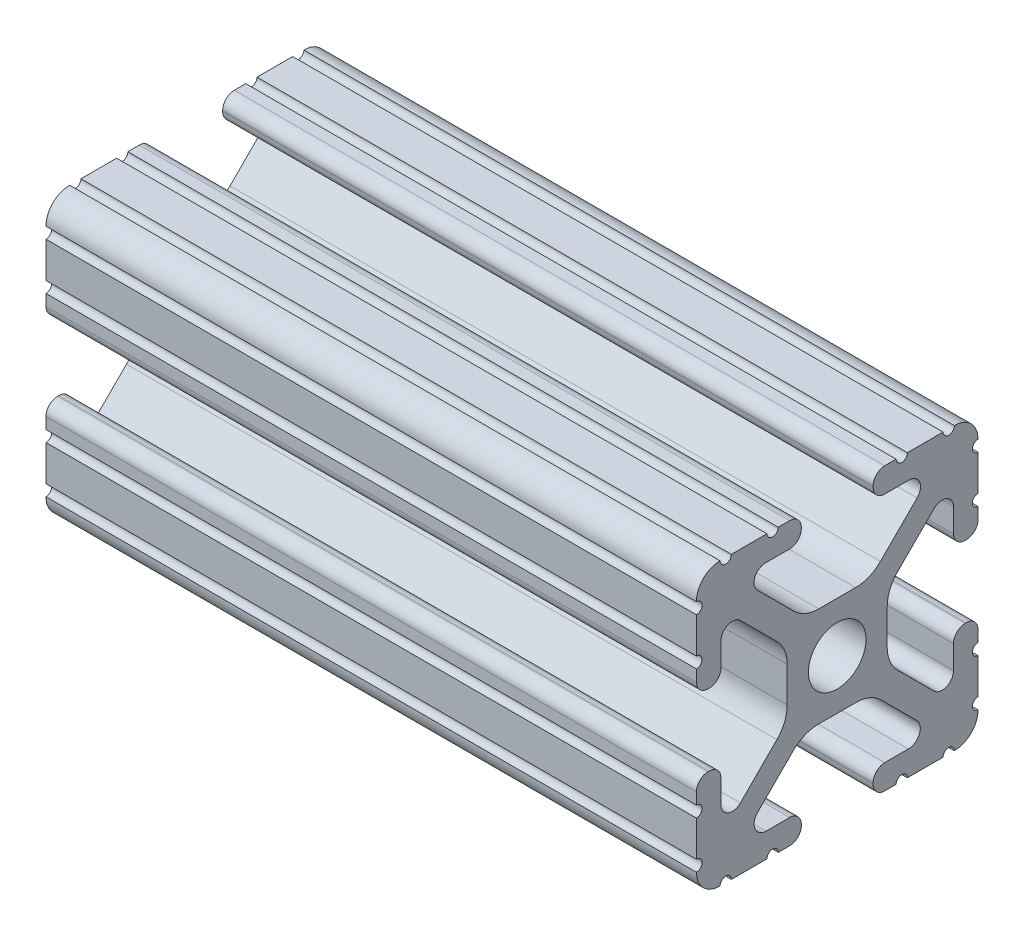
SolidWorks part; units mm, degrees
ref_plane "Front Plane" through (0, 0, 0) normal (0, 0, 1) x (1, 0, 0)
ref_plane "Top Plane" through (0, 0, 0) normal (0, 1, 0) x (1, 0, 0)
ref_plane "Right Plane" through (0, 0, 0) normal (1, 0, 0) x (0, 0, -1)
sketch "Sketch1" plane through (0, 0, 0) normal (0, 1, 0) x (1, 0, 0)
  line L0 (0, 0) -> (-58.674, 0)
  dimension "D1" = 58.674
other "10 1010 PROFILE(1)"
ref_plane "Plane1" through (0, 0, 0) normal (-1, 0, 0) x (0, 0, 1)
sketch "Sketch11" plane through (0, 0, 0) normal (-1, 0, 0) x (0, 0, 1)
  line L1 (12.7, 12.7) -> (-12.7, 12.7) construction
  line L2 (12.7, 12.7) -> (12.7, -12.7) construction
  line L3 (12.7, -12.7) -> (-12.7, -12.7) construction
  line L4 (-12.7, 12.7) -> (-12.7, -12.7) construction
  line L5 (12.7, 12.7) -> (-12.7, -12.7) construction
  line L6 (12.7, -12.7) -> (-12.7, 12.7) construction
  line L88 (-1.7093, -4.4958) -> (1.7093, -4.4958)
  line L89 (3.9523, -5.4237) -> (7.1797, -8.6452)
  line L90 (6.4164, -10.4902) -> (4.2875, -10.4902)
  line L91 (3.2385, -11.5392) -> (3.2385, -11.651)
  line L92 (4.2875, -12.7) -> (5.3171, -12.7)
  line L93 (6.3331, -12.7) -> (9.5504, -12.7)
  line L94 (12.7, -9.5504) -> (12.7, -6.3331)
  line L95 (12.7, -5.3171) -> (12.7, -4.2875)
  line L96 (11.651, -3.2385) -> (11.5392, -3.2385)
  line L97 (10.4902, -4.2875) -> (10.4902, -6.4021)
  line L98 (8.737, -7.1292) -> (5.4405, -3.8388)
  line L99 (4.5085, -1.5917) -> (4.5085, 1.5917)
  line L100 (5.4405, 3.8388) -> (8.737, 7.1292)
  line L101 (10.4902, 6.4021) -> (10.4902, 4.2875)
  line L102 (11.5392, 3.2385) -> (11.651, 3.2385)
  line L103 (12.7, 4.2875) -> (12.7, 5.3171)
  line L104 (12.7, 6.3331) -> (12.7, 9.5504)
  line L105 (9.5504, 12.7) -> (6.3331, 12.7)
  line L106 (5.3171, 12.7) -> (4.2875, 12.7)
  line L107 (3.2384, 11.651) -> (3.2384, 11.5392)
  line L108 (4.2875, 10.4902) -> (6.4768, 10.4902)
  line L109 (7.2072, 8.7245) -> (3.9003, 5.4237)
  line L110 (1.6573, 4.4958) -> (-1.6573, 4.4958)
  line L111 (-3.9003, 5.4237) -> (-7.2072, 8.7245)
  line L112 (-6.4768, 10.4902) -> (-4.2875, 10.4902)
  line L113 (-3.2384, 11.5392) -> (-3.2384, 11.651)
  line L114 (-4.2875, 12.7) -> (-5.3171, 12.7)
  line L115 (-6.3331, 12.7) -> (-9.5504, 12.7)
  line L116 (-12.7, 9.5504) -> (-12.7, 6.3331)
  line L117 (-12.7, 5.3171) -> (-12.7, 4.2875)
  line L118 (-11.651, 3.2385) -> (-11.5392, 3.2385)
  line L119 (-10.4902, 4.2875) -> (-10.4902, 6.4021)
  line L120 (-8.737, 7.1292) -> (-5.4405, 3.8388)
  line L121 (-4.5085, 1.5917) -> (-4.5085, -1.5917)
  line L122 (-5.4405, -3.8388) -> (-8.737, -7.1292)
  line L123 (-10.4902, -6.4021) -> (-10.4902, -4.2875)
  line L124 (-11.5392, -3.2385) -> (-11.651, -3.2385)
  line L125 (-12.7, -4.2875) -> (-12.7, -5.3171)
  line L126 (-12.7, -6.3331) -> (-12.7, -9.5504)
  line L127 (-9.5504, -12.7) -> (-6.3331, -12.7)
  line L128 (-5.3171, -12.7) -> (-4.2875, -12.7)
  line L129 (-3.2385, -11.651) -> (-3.2385, -11.5392)
  line L130 (-4.2875, -10.4902) -> (-6.4164, -10.4902)
  line L131 (-7.1797, -8.6452) -> (-3.9523, -5.4237)
  circle A1 centre (0, 0) radius 2.6035
  arc A104 (-1.7093, -4.4958) -> (-3.9523, -5.4237) centre (-1.7093, -7.6708) ccw
  arc A105 (3.9523, -5.4237) -> (1.7093, -4.4958) centre (1.7093, -7.6708) ccw
  arc A106 (6.4164, -10.4902) -> (7.1797, -8.6452) centre (6.4164, -9.4098) ccw
  arc A107 (4.2875, -10.4902) -> (3.2385, -11.5392) centre (4.2875, -11.5392) ccw
  arc A108 (3.2385, -11.651) -> (4.2875, -12.7) centre (4.2875, -11.651) ccw
  arc A109 (6.3331, -12.7) -> (5.3171, -12.7) centre (5.8251, -12.7) ccw
  arc A110 (10.5664, -12.6998) -> (9.5504, -12.7) centre (10.0584, -12.7) ccw
  arc A111 (10.5664, -12.6998) -> (12.6998, -10.5664) centre (10.5918, -10.5918) ccw
  arc A112 (12.7, -9.5504) -> (12.6998, -10.5664) centre (12.7, -10.0584) ccw
  arc A113 (12.7, -5.3171) -> (12.7, -6.3331) centre (12.7, -5.8251) ccw
  arc A114 (12.7, -4.2875) -> (11.651, -3.2385) centre (11.651, -4.2875) ccw
  arc A115 (11.5392, -3.2385) -> (10.4902, -4.2875) centre (11.5392, -4.2875) ccw
  arc A116 (8.737, -7.1292) -> (10.4902, -6.4021) centre (9.4628, -6.4021) ccw
  arc A117 (4.5085, -1.5917) -> (5.4405, -3.8388) centre (7.6835, -1.5917) ccw
  arc A118 (5.4405, 3.8388) -> (4.5085, 1.5917) centre (7.6835, 1.5917) ccw
  arc A119 (10.4902, 6.4021) -> (8.737, 7.1292) centre (9.4628, 6.4021) ccw
  arc A120 (10.4902, 4.2875) -> (11.5392, 3.2385) centre (11.5392, 4.2875) ccw
  arc A121 (11.651, 3.2385) -> (12.7, 4.2875) centre (11.651, 4.2875) ccw
  arc A122 (12.7, 6.3331) -> (12.7, 5.3171) centre (12.7, 5.8251) ccw
  arc A123 (12.6998, 10.5664) -> (12.7, 9.5504) centre (12.7, 10.0584) ccw
  arc A124 (12.6998, 10.5664) -> (10.5664, 12.6998) centre (10.5918, 10.5918) ccw
  arc A125 (9.5504, 12.7) -> (10.5664, 12.6998) centre (10.0584, 12.7) ccw
  arc A126 (5.3171, 12.7) -> (6.3331, 12.7) centre (5.8251, 12.7) ccw
  arc A127 (4.2875, 12.7) -> (3.2384, 11.651) centre (4.2875, 11.651) ccw
  arc A128 (3.2384, 11.5392) -> (4.2875, 10.4902) centre (4.2875, 11.5392) ccw
  arc A129 (7.2072, 8.7245) -> (6.4768, 10.4902) centre (6.4768, 9.4563) ccw
  arc A130 (1.6573, 4.4958) -> (3.9003, 5.4237) centre (1.6573, 7.6708) ccw
  arc A131 (-3.9003, 5.4237) -> (-1.6573, 4.4958) centre (-1.6573, 7.6708) ccw
  arc A132 (-6.4768, 10.4902) -> (-7.2072, 8.7245) centre (-6.4768, 9.4563) ccw
  arc A133 (-4.2875, 10.4902) -> (-3.2384, 11.5392) centre (-4.2875, 11.5392) ccw
  arc A134 (-3.2384, 11.651) -> (-4.2875, 12.7) centre (-4.2875, 11.651) ccw
  arc A135 (-6.3331, 12.7) -> (-5.3171, 12.7) centre (-5.8251, 12.7) ccw
  arc A136 (-10.5664, 12.6998) -> (-9.5504, 12.7) centre (-10.0584, 12.7) ccw
  arc A137 (-10.5664, 12.6998) -> (-12.6998, 10.5664) centre (-10.5918, 10.5918) ccw
  arc A138 (-12.7, 9.5504) -> (-12.6998, 10.5664) centre (-12.7, 10.0584) ccw
  arc A139 (-12.7, 5.3171) -> (-12.7, 6.3331) centre (-12.7, 5.8251) ccw
  arc A140 (-12.7, 4.2875) -> (-11.651, 3.2385) centre (-11.651, 4.2875) ccw
  arc A141 (-11.5392, 3.2385) -> (-10.4902, 4.2875) centre (-11.5392, 4.2875) ccw
  arc A142 (-8.737, 7.1292) -> (-10.4902, 6.4021) centre (-9.4628, 6.4021) ccw
  arc A143 (-4.5085, 1.5917) -> (-5.4405, 3.8388) centre (-7.6835, 1.5917) ccw
  arc A144 (-5.4405, -3.8388) -> (-4.5085, -1.5917) centre (-7.6835, -1.5917) ccw
  arc A145 (-10.4902, -6.4021) -> (-8.737, -7.1292) centre (-9.4628, -6.4021) ccw
  arc A146 (-10.4902, -4.2875) -> (-11.5392, -3.2385) centre (-11.5392, -4.2875) ccw
  arc A147 (-11.651, -3.2385) -> (-12.7, -4.2875) centre (-11.651, -4.2875) ccw
  arc A148 (-12.7, -6.3331) -> (-12.7, -5.3171) centre (-12.7, -5.8251) ccw
  arc A149 (-12.6998, -10.5664) -> (-12.7, -9.5504) centre (-12.7, -10.0584) ccw
  arc A150 (-12.6998, -10.5664) -> (-10.5664, -12.6998) centre (-10.5918, -10.5918) ccw
  arc A151 (-9.5504, -12.7) -> (-10.5664, -12.6998) centre (-10.0584, -12.7) ccw
  arc A152 (-5.3171, -12.7) -> (-6.3331, -12.7) centre (-5.8251, -12.7) ccw
  arc A153 (-4.2875, -12.7) -> (-3.2385, -11.651) centre (-4.2875, -11.651) ccw
  arc A154 (-3.2385, -11.5392) -> (-4.2875, -10.4902) centre (-4.2875, -11.5392) ccw
  arc A155 (-7.1797, -8.6452) -> (-6.4164, -10.4902) centre (-6.4164, -9.4098) ccw
  point P3 (0, 0)
  point P21 (-12.7, 0)
  point P22 (0, 12.7)
  point P25 (12.7, 0)
  point P28 (0, -12.7)
  point P30 (-12.7, -12.7)
  point P33 (12.7, -12.7)
  point P37 (12.7, 12.7)
  point P40 (-12.7, 12.7)
  point P43 (0, 0)
  dimension "D1" = 25.4
sketch "Sketch13" plane through (0, 0, 12.7) normal (0, 0, 1) x (1, 0, 0)
  line L0 (0, 0) -> (-58.674, 0) construction
  line L1 (-58.674, 6.3331) -> (-58.674, 9.5504) construction
  line L2 (0, 6.3331) -> (0, 9.5504) construction
  circle A0 centre (-39.624, 0) radius 2.54
  circle A1 centre (-19.05, 0) radius 2.54
  point P0 (-39.624, 0)
  point P1 (-19.05, 0)
  dimension "D3" = 5.08
  dimension "D4" = 5.08
  dimension "D1" = 19.05
  dimension "D2" = 19.05
extrude "Cut-Extrude1" cut sketch "Sketch13" against normal through all
